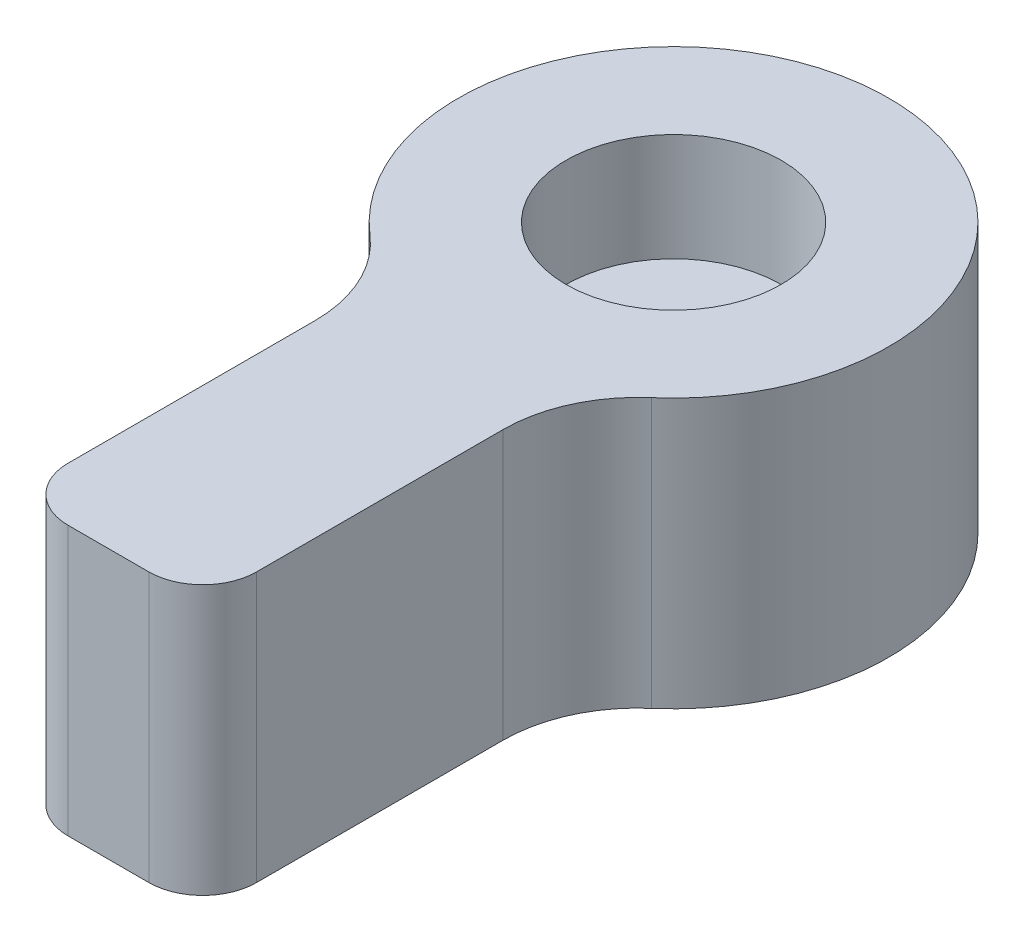
SolidWorks part; units mm, degrees
material "Сплав 2024"
ref_plane "Спереди" through (0, 0, 0) normal (0, 0, 1) x (1, 0, 0)
ref_plane "Сверху" through (0, 0, 0) normal (0, 1, 0) x (1, 0, 0)
ref_plane "Справа" through (0, 0, 0) normal (1, 0, 0) x (0, 0, -1)
sketch "Эскиз1" plane through (0, 0, 0) normal (0, 1, 0) x (1, 0, 0)
  line L0 (0, 18.3103) -> (0, -37.454) construction
  line L3 (-3.5, -7.1937) -> (-3.5, -21)
  line L4 (-3.5, -21) -> (3.5, -21)
  line L5 (3.5, -7.1937) -> (3.5, -21)
  arc A0 (3.5, -7.1937) -> (-3.5, -7.1937) centre (0, 0) ccw
  point P1 (0, -21)
  dimension "D1" = 16
  dimension "D2" = 7
  dimension "D3" = 21
extrude "Бобышка-Вытянуть1" add sketch "Эскиз1" along normal blind 10
hole_wizard "Цековка для винта с внутренним шестигранником M41" [suppressed] positions "Эскиз3" profile "Эскиз2" counterbore size "M4" standard "Ansi Metric"
sketch "Эскиз3" plane through (0, 10, 0) normal (0, 1, 0) x (1, 0, 0)
  point P0 (0, 0)
sketch "Эскиз2" plane through (0, 10, 0) normal (1, 0, 0) x (0, 0, 1)
  line L0 (0, 0) -> (0, 10)
  line L1 (0, 10) -> (2.25, 10)
  line L3 (2.25, 10) -> (2.25, 4)
  line L4 (2.25, 4) -> (4, 4)
  line L5 (4, 4) -> (4, 0)
  line L7 (4, 0) -> (0, 0)
  line L11 (0, -6.35) -> (0, 107.95) construction
  dimension "Диаметр сквозного отверстия" = 4.5
  dimension "Глубина сквозного отверстия" = 10
  dimension "Диаметр цековки" = 8
  dimension "Глубина цековки" = 4
fillet "Скругление1" radius 2 2 edges at (3.5, 5, 21) (-3.5, 5, 21)
fillet "Скругление2" radius 5 2 edges at (3.5, 5, 7.1937) (-3.5, 5, 7.1937)
chamfer "Фаска1" [suppressed] distance 0.5 angle 45
sketch "Эскиз4" plane through (0, 10, 0) normal (0, 1, 0) x (1, 0, 0)
  circle A0 centre (0, 0) radius 4
  dimension "D1" = 8
extrude "Вырез-Вытянуть1" cut sketch "Эскиз4" against normal blind 4
hole_wizard "Отверстие обработанное метчиком M4x0.71" positions "Эскиз6" profile "Эскиз5" tap size "M4x0.7" standard "Ansi Metric" end condition through all
sketch "Эскиз6" plane through (0, 6, 0) normal (0, 1, 0) x (1, 0, 0)
  point P0 (0, 0)
sketch "Эскиз5" plane through (0, 6, 0) normal (1, 0, 0) x (0, 0, 1)
  line L0 (0, 0) -> (0, 6)
  line L1 (0, 6) -> (1.65, 6)
  line L2 (1.65, 6) -> (1.65, 0)
  line L5 (1.65, 0) -> (0, 0)
  line L11 (0, -6.35) -> (0, 107.95) construction
  dimension "Диаметр проходного сверла" = 3.3
  dimension "Глубина проходного сверла" = 6
cosmetic thread "Отверстие резьбы1" parameters "D2"=4
